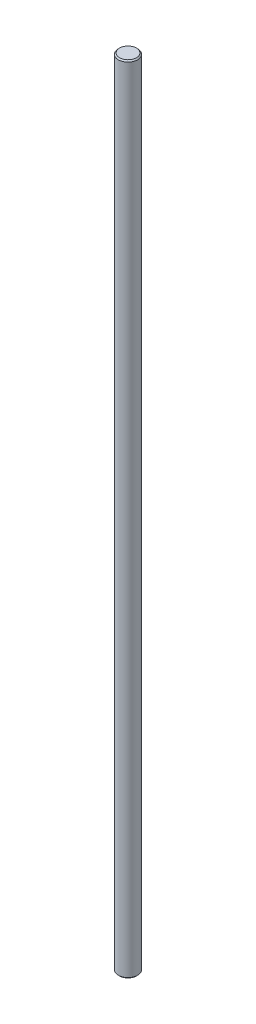
SolidWorks part; units mm, degrees
ref_plane "Front Plane" through (0, 0, 0) normal (0, 0, 1) x (1, 0, 0)
ref_plane "Top Plane" through (0, 0, 0) normal (0, 1, 0) x (1, 0, 0)
ref_plane "Right Plane" through (0, 0, 0) normal (1, 0, 0) x (0, 0, -1)
sketch "Sketch1" plane through (0, 0, 0) normal (0, 1, 0) x (1, 0, 0)
  circle A0 centre (0, 0) radius 4
  dimension "D1" = 8
extrude "Boss-Extrude1" add sketch "Sketch1" along normal blind 330.2
chamfer "Chamfer1" distance 0.5 angle 45 2 edges at (0, 0, 4) (0, 330.2, 4)
